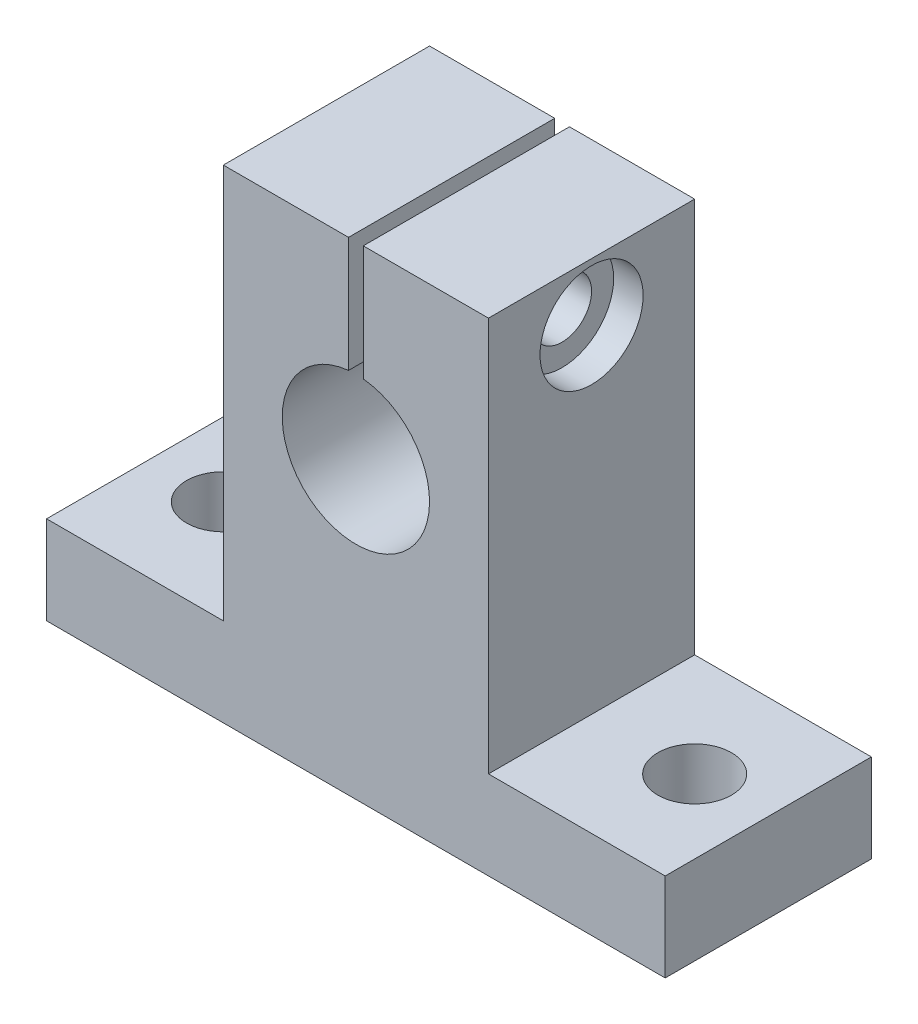
SolidWorks part; units mm, degrees
ref_plane "前视基准面" through (0, 0, 0) normal (0, 0, 1) x (1, 0, 0)
ref_plane "上视基准面" through (0, 0, 0) normal (0, 1, 0) x (1, 0, 0)
ref_plane "右视基准面" through (0, 0, 0) normal (1, 0, 0) x (0, 0, -1)
sketch "草图1" plane through (0, 0, 0) normal (0, 0, 1) x (1, 0, 0)
  line L0 (0, 0) -> (0, 255.3694) construction
  line L1 (21, 0) -> (-21, 0)
  line L2 (-21, 0) -> (-21, 6)
  line L3 (-21, 6) -> (-9, 6)
  line L4 (-9, 6) -> (-9, 32.8)
  line L5 (-9, 32.8) -> (9, 32.8)
  line L6 (21, 0) -> (21, 6)
  line L7 (9, 6) -> (9, 32.8)
  line L8 (21, 6) -> (9, 6)
  circle A0 centre (0, 20) radius 5
  point P13 (0, 32.8)
  dimension "D5" = 10
  dimension "D1" = 21
  dimension "D2" = 6
  dimension "D3" = 32.8
  dimension "D4" = 18
  dimension "D6" = 20
extrude "凸台-拉伸1" add sketch "草图1" along normal blind 14
sketch "草图2" plane through (0, 6, 0) normal (0, 1, 0) x (1, 0, 0)
  line L0 (-21, -7) -> (-9, -7) construction
  line L1 (-21, -14) -> (-21, 0) construction
  line L2 (-9, -14) -> (-9, 0) construction
  line L3 (0, 0) -> (0, -14) construction
  line L4 (9, -14) -> (-9, -14) construction
  circle A0 centre (-16, -7) radius 2.5
  circle A1 centre (16, -7) radius 2.5
  dimension "D1" = 5
  dimension "D2" = 5
extrude "切除-拉伸1" cut sketch "草图2" against normal through all
sketch "草图3" plane through (0, 32.8, 0) normal (0, 1, 0) x (1, 0, 0)
  line L0 (0, 0) -> (0, -14) construction
  line L1 (9, 0) -> (-9, 0) construction
  line L2 (9, -14) -> (-9, -14) construction
  line L4 (-0.5, 0) -> (0.5, 0)
  line L5 (-0.5, 0) -> (-0.5, -14)
  line L6 (-0.5, -14) -> (0.5, -14)
  line L7 (0.5, 0) -> (0.5, -14)
  dimension "D1" = 1
extrude "切除-拉伸2" cut sketch "草图3" against normal blind 14
sketch "草图4" plane through (-0.5, 0, 0) normal (1, 0, 0) x (0, 0, -1)
  line L0 (-14, 24.9749) -> (0, 24.9749) construction
  line L1 (-14, 24.9749) -> (0, 24.9749) construction
  line L2 (-7, 24.9749) -> (-7, 32.8) construction
  line L3 (-14, 32.8) -> (0, 32.8) construction
  circle A0 centre (-7, 28.8875) radius 2
  dimension "D1" = 4
extrude "切除-拉伸3" cut sketch "草图4" against normal mid plane 20
sketch "草图5" plane through (9, 0, 0) normal (1, 0, 0) x (0, 0, -1)
  circle A0 centre (-7, 28.8875) radius 3.5
  dimension "D1" = 7
extrude "切除-拉伸4" cut sketch "草图5" against normal blind 2
